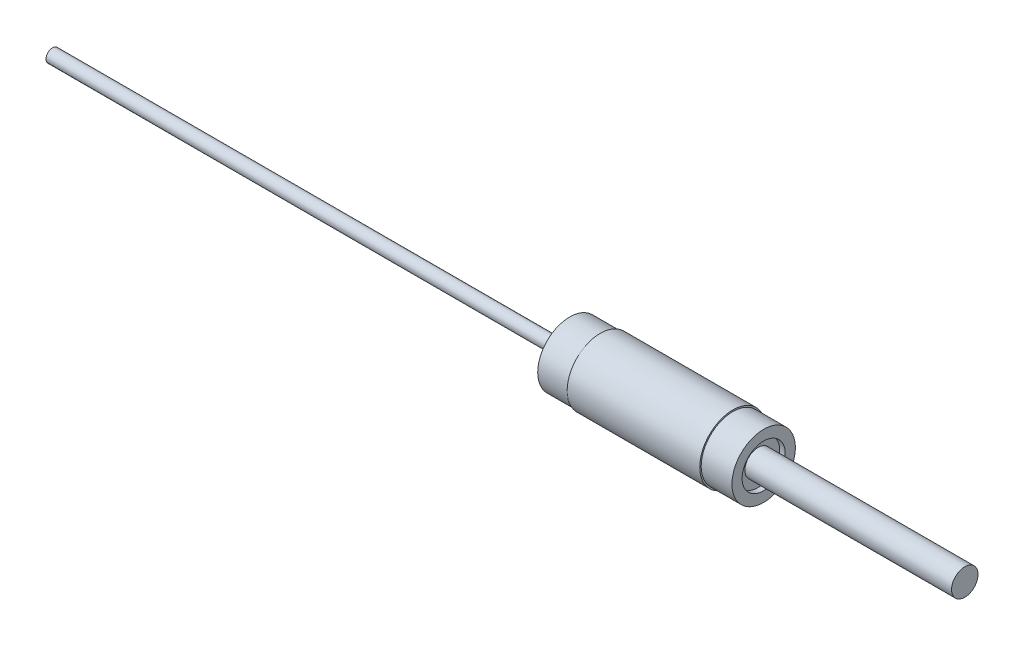
SolidWorks part; units mm, degrees
ref_plane "Front Plane" through (0, 0, 0) normal (0, 0, 1) x (1, 0, 0)
ref_plane "Top Plane" through (0, 0, 0) normal (0, 1, 0) x (1, 0, 0)
ref_plane "Right Plane" through (0, 0, 0) normal (1, 0, 0) x (0, 0, -1)
ref_axis "Axis1" through (-88.99, 0, 0) along (1, 0, 0)
sketch "Sketch2" plane through (0, 0, 0) normal (0, 0, 1) x (1, 0, 0)
  line L0 (0, 1.59) -> (-126, 1.59)
  line L1 (-88.99, 0) -> (88.99, 0) construction
  line L2 (0, 3.35) -> (0, 7.8)
  line L3 (0, 7.8) -> (7.45, 7.8)
  line L4 (0, 3.35) -> (3.95, 3.35) construction
  line L5 (3.95, 3.35) -> (3.95, 5.65) construction
  line L6 (3.95, 5.65) -> (7.45, 5.65) construction
  line L7 (7.45, 5.65) -> (7.45, 7.8) construction
  line L8 (47.25, 7.725) -> (39.75, 7.725)
  line L9 (39.75, 3.375) -> (45.9, 3.375) construction
  line L10 (45.9, 5.25) -> (47.25, 5.25)
  line L11 (47.25, 5.25) -> (47.25, 7.725)
  line L12 (45.9, 5.25) -> (45.9, 3.375)
  line L13 (39.75, 3.375) -> (39.75, 7.725) construction
  line L14 (96.25, 3.225) -> (45.9, 3.225)
  line L15 (45.9, 3.225) -> (45.9, 3.375)
  line L16 (96.25, 3.225) -> (96.25, 0)
  line L17 (96.25, 0) -> (-126, 0)
  line L18 (-126, 0) -> (-126, 1.59)
  line L19 (7.45, 8.075) -> (39.75, 8.075)
  line L20 (7.45, 7.8) -> (7.45, 8.075)
  line L21 (39.75, 8.075) -> (39.75, 7.725)
  line L22 (0, 1.59) -> (0, 3.35)
  point P13 (0, 5.575)
  dimension "D1" = 126
  dimension "D2" = 1.59
  dimension "D3" = 3.35
  dimension "D4" = 7.8
  dimension "D5" = 7.45
  dimension "D6" = 5.65
  dimension "D7" = 3.5
  dimension "D8" = 47.25
  dimension "D9" = 7.5
  dimension "D10" = 7.725
  dimension "D11" = 3.375
  dimension "D12" = 5.25
  dimension "D13" = 1.35
  dimension "D14" = 49
  dimension "D15" = 3.225
  dimension "D16" = 8.075
revolve "Revolve1" add sketch "Sketch2" angle 360 about axis through (-88.99, 0, 0) along (1, 0, 0)
